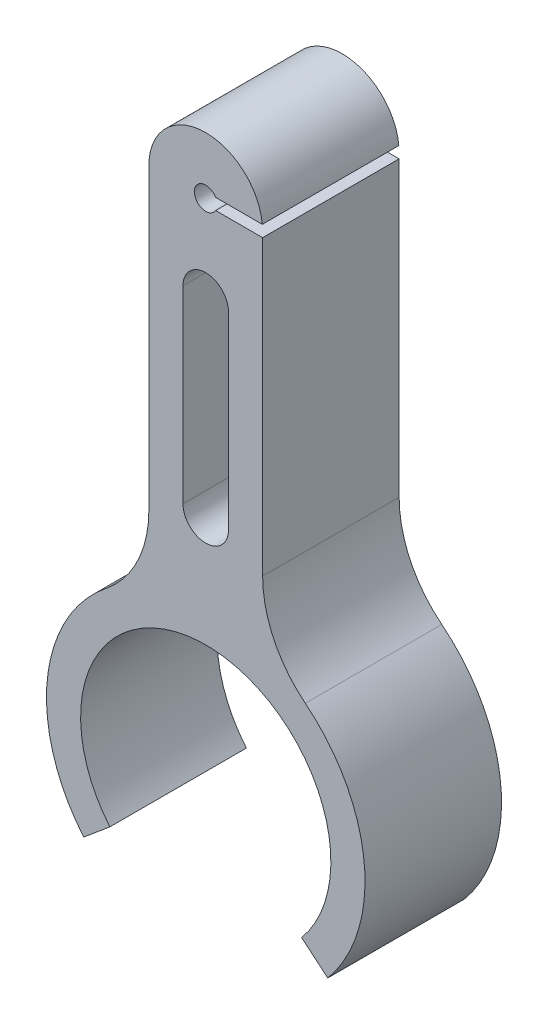
SolidWorks part; units mm, degrees
ref_plane "Front Plane" through (0, 0, 0) normal (0, 0, 1) x (1, 0, 0)
ref_plane "Top Plane" through (0, 0, 0) normal (0, 1, 0) x (1, 0, 0)
ref_plane "Right Plane" through (0, 0, 0) normal (1, 0, 0) x (0, 0, -1)
sketch "Sketch1" plane through (0, 0, 0) normal (0, 0, 1) x (1, 0, 0)
  line L0 (5, 45) -> (5, 13.0767)
  line L1 (-5, 45) -> (-5, 13.0767)
  line L2 (0, 0) -> (-17.2463, -14.4714)
  line L3 (0, 0) -> (16.3651, -13.7319)
  line L4 (0, 0) -> (0, -26.7503) construction
  line L5 (-5, 29.0383) -> (5, 29.0383) construction
  line L6 (0, 37.3356) -> (0, 20.7411) construction
  line L7 (2, 37.3356) -> (2, 20.7411)
  line L8 (-2, 37.3356) -> (-2, 20.7411)
  circle A0 centre (0, 0) radius 11
  circle A1 centre (0, 45) radius 2
  arc A2 (5, 45) -> (-5, 45) centre (0, 45) ccw
  arc A3 (-5, 13.0767) -> (5, 13.0767) centre (0, 0) ccw
  arc A4 (2, 37.3356) -> (-2, 37.3356) centre (0, 37.3356) ccw
  arc A5 (-2, 20.7411) -> (2, 20.7411) centre (0, 20.7411) ccw
  point P16 (0, 29.0383)
  dimension "D2" = 4
  dimension "D3" = 22
  dimension "D4" = 3
  dimension "D5" = 3
  dimension "D8" = 2
  dimension "D1" = 45
  dimension "D6" = 50
  dimension "D7" = 50
extrude "Boss-Extrude1" add sketch "Sketch1" along normal blind 12 contours L1 A3 L2 A0 L3 L0 A2 A5 L8 A4 L7 A1
sketch "Sketch2" plane through (0, 0, 12) normal (0, 0, 1) x (1, 0, 0)
  circle A0 centre (0, 45) radius 2
  circle A1 centre (0, 45) radius 1
  dimension "D1" = 2
extrude "Boss-Extrude2" add sketch "Sketch2" against normal blind 3
fillet "Fillet1" radius 10 2 edges at (5, 13.0767, 6) (-5, 13.0767, 6)
sketch "Sketch3" plane through (5, 0, 0) normal (1, 0, 0) x (0, 0, -1)
  line L0 (-12, 45) -> (0, 45)
extrude "Cut-Extrude-Thin2" cut sketch "Sketch3" against normal blind 5 and the other way through all thin thin type mid plane wall 1
